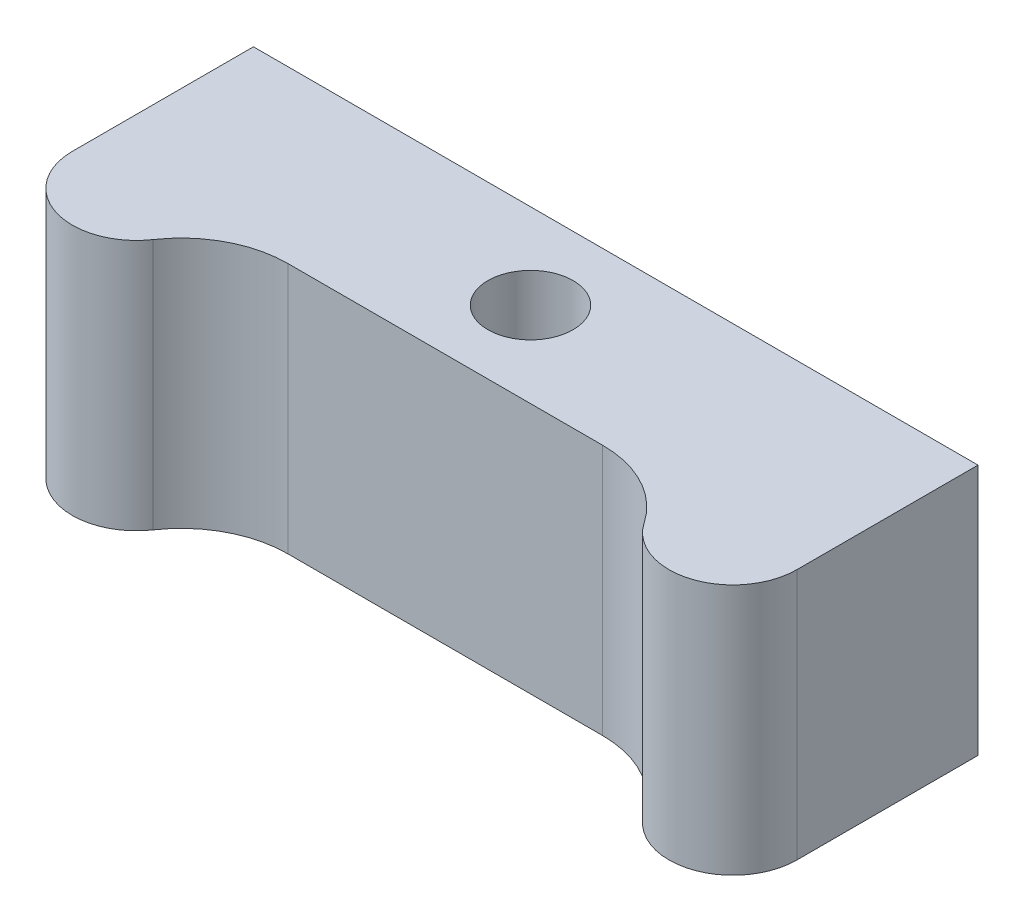
SolidWorks part; units mm, degrees
ref_plane "Front Plane" through (0, 0, 0) normal (0, 0, 1) x (1, 0, 0)
ref_plane "Top Plane" through (0, 0, 0) normal (0, 1, 0) x (1, 0, 0)
ref_plane "Right Plane" through (0, 0, 0) normal (1, 0, 0) x (0, 0, -1)
sketch "Sketch1" plane through (0, 0, 0) normal (0, 1, 0) x (1, 0, 0)
  line L1 (7.3856, -4) -> (-7.3856, -4)
  line L2 (17, -4.5) -> (17, 4)
  line L3 (17, 4) -> (-17, 4)
  line L4 (-17, -4.5) -> (-17, 4)
  arc A1 (-17, -4.5) -> (-11.5196, -6.1875) centre (-14, -4.5) ccw
  arc A3 (11.5196, -6.1875) -> (17, -4.5) centre (14, -4.5) ccw
  arc A4 (-7.3856, -4) -> (-11.5196, -6.1875) centre (-7.3856, -9) ccw
  arc A5 (11.5196, -6.1875) -> (7.3856, -4) centre (7.3856, -9) ccw
  point P0 (0, 0)
  point P2 (-17, -4)
  point P4 (0, 0)
  point P9 (-17, -5.8742)
  point P11 (-17, -4)
  point P13 (0, 0)
  point P23 (-16.9923, -4.7145)
  point P24 (-11, -4)
  point P25 (-11, -4.5)
  dimension "D3" = 3
  dimension "D4" = 3
  dimension "D7" = 0.5
  dimension "D8" = 0.5
  dimension "D5" = 17
  dimension "D12" = 10
  dimension "D13" = 10
  dimension "D9" = 3
  dimension "D2" = 34
  dimension "D6" = 4
  dimension "D10" = 3
  dimension "D11" = 4
extrude "Boss-Extrude1" add sketch "Sketch1" along normal blind 11.8
sketch "Sketch2" plane through (0, 11.8, 0) normal (0, 1, 0) x (1, 0, 0)
  circle A0 centre (0, 0) radius 2
  point P3 (0, 0)
  dimension "D1" = 4
extrude "Cut-Extrude1" cut sketch "Sketch2" against normal through all
